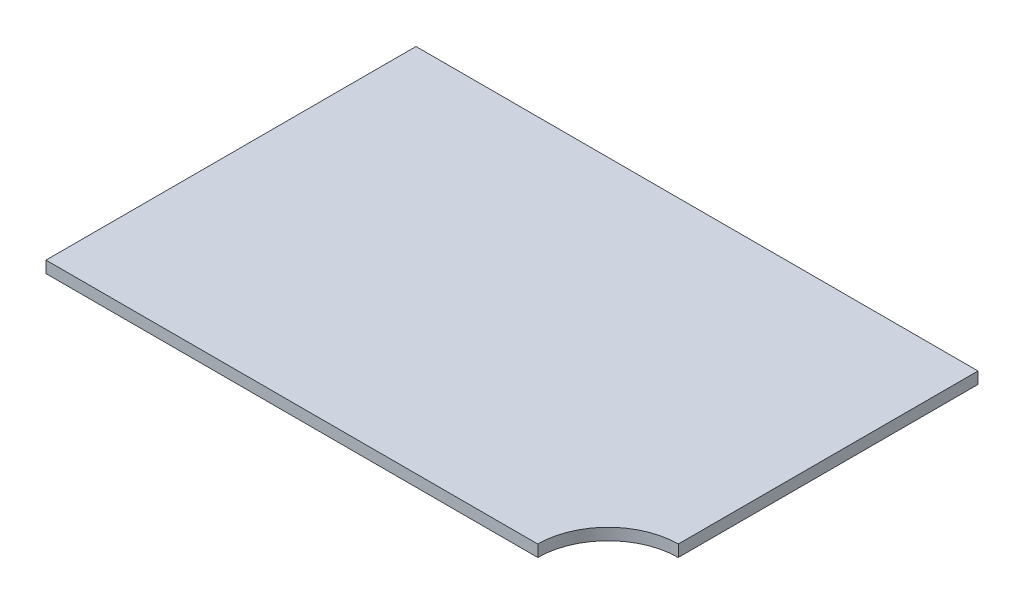
SolidWorks part; units mm, degrees
ref_plane "Front Plane" through (0, 0, 0) normal (0, 0, 1) x (1, 0, 0)
ref_plane "Top Plane" through (0, 0, 0) normal (0, 1, 0) x (1, 0, 0)
ref_plane "Right Plane" through (0, 0, 0) normal (1, 0, 0) x (0, 0, -1)
sketch "Sketch1" plane through (0, 0, 0) normal (0, 1, 0) x (1, 0, 0)
  line L1 (-120, 0) -> (120, 0)
  line L2 (-120, 0) -> (-120, -158)
  line L3 (-120, -158) -> (120, -158)
  line L4 (120, 0) -> (120, -158)
  point P4 (0, 0)
  dimension "D1" = 240
  dimension "D2" = 158
extrude "Boss-Extrude1" add sketch "Sketch1" along normal blind 5
sketch "Sketch2" plane through (0, 0, 0) normal (0, -1, 0) x (1, 0, 0)
  line L0 (-120, 0) -> (-120, 158) construction
  line L1 (120, 0) -> (-120, 0) construction
  line L2 (120, 0) -> (120, 40) construction
  line L3 (120, 40) -> (-120, 40) construction
  line L4 (-120, 0) -> (-120, 40) construction
  line L5 (120, 20) -> (0, 20) construction
  line L6 (0, 40) -> (0, 0) construction
  line L7 (0, 20) -> (-120, 20) construction
  point P12 (60, 20)
  point P14 (-60, 20)
  dimension "D1" = 40
hole_wizard "CBORE for M4 SHCS1" positions "Sketch2" profile "Sketch3" counterbore size "M4" standard "ANSI Metric"
sketch "Sketch3" plane through (-18.75, 0, 20) normal (1, 0, 0) x (0, 0, -1)
  line L0 (0, 0) -> (0, 5)
  line L1 (0, 5) -> (2.25, 5)
  line L3 (2.25, 5) -> (2.25, 4)
  line L4 (2.25, 4) -> (4, 4)
  line L5 (4, 4) -> (4, 0)
  line L7 (4, 0) -> (0, 0)
  line L11 (0, -6.35) -> (0, 107.95) construction
  dimension "Thru Hole Dia." = 4.5
  dimension "Thru Hole Depth" = 5
  dimension "C'Bore Dia." = 8
  dimension "C'Bore Depth" = 4
sketch "Sketch4" plane through (0, 5, 0) normal (0, 1, 0) x (1, 0, 0)
  line L0 (0, 0) -> (0, -158) construction
  line L1 (-120, -158) -> (120, -158) construction
  line L2 (0, -79) -> (120, -79) construction
  line L3 (120, -158) -> (120, 0) construction
  point P9 (159.1973, -79)
  dimension "D1" = 159.1973
sketch "Sketch5" plane through (0, 0, 0) normal (0, -1, 0) x (1, 0, 0)
  line L0 (120, 158) -> (120, 0) construction
  line L1 (-120, 158) -> (120, 158) construction
  line L2 (120, 158) -> (120, 128)
  line L3 (120, 158) -> (90, 158)
  line L4 (120, 128) -> (96.5878, 128) construction
  arc A0 (120, 128) -> (90, 158) centre (120, 158) cw
  dimension "D1" = 30
  dimension "D2" = 30
extrude "Cut-Extrude1" cut sketch "Sketch5" against normal through all
equation "\"D2@Sketch5\"=\"D1@Sketch5\""
